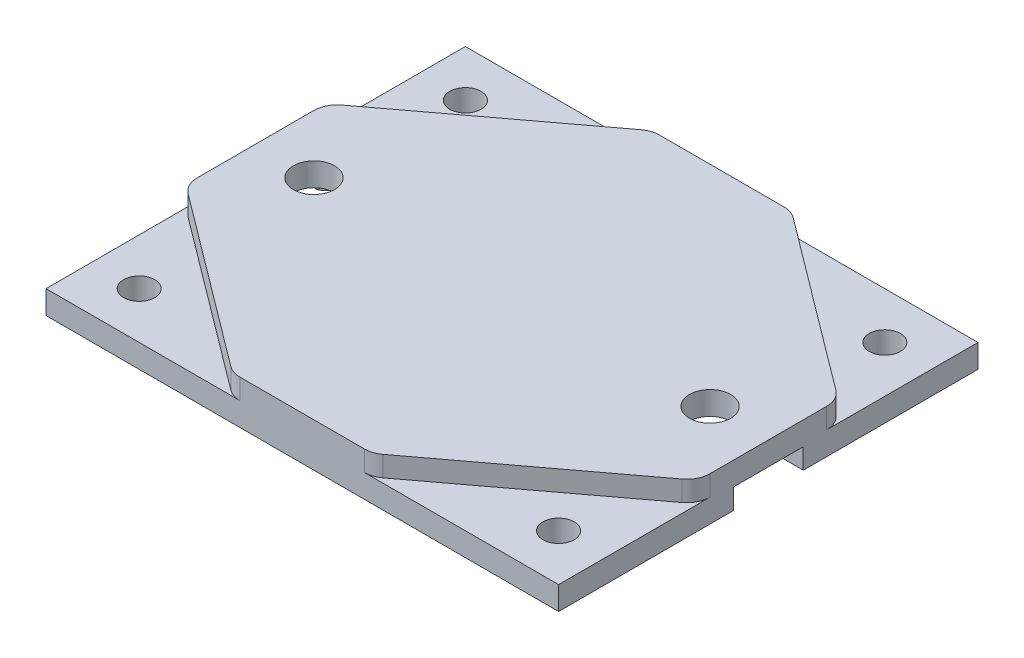
SolidWorks part; units mm, degrees
ref_plane "Front Plane" through (0, 0, 0) normal (0, 0, 1) x (1, 0, 0)
ref_plane "Top Plane" through (0, 0, 0) normal (0, 1, 0) x (1, 0, 0)
ref_plane "Right Plane" through (0, 0, 0) normal (1, 0, 0) x (0, 0, -1)
sketch "Sketch1" plane through (0, 0, 0) normal (0, 1, 0) x (1, 0, 0)
  line L1 (0, 0) -> (55.88, 0)
  line L2 (0, 0) -> (0, 45.72)
  line L3 (0, 45.72) -> (55.88, 45.72)
  line L4 (55.88, 0) -> (55.88, 45.72)
  dimension "D1" = 55.88
  dimension "D2" = 45.72
extrude "Boss-Extrude1" add sketch "Sketch1" along normal blind 2.54
sketch "Sketch2" plane through (0, 2.54, 0) normal (0, 1, 0) x (1, 0, 0)
  line L0 (0, 45.72) -> (0, 0) construction
  line L1 (5.08, 40.64) -> (50.8, 40.64) construction
  line L2 (5.08, 40.64) -> (5.08, 5.08) construction
  line L3 (5.08, 5.08) -> (50.8, 5.08) construction
  line L4 (50.8, 40.64) -> (50.8, 5.08) construction
  line L5 (55.88, 0) -> (55.88, 45.72) construction
  line L6 (0, 0) -> (55.88, 0) construction
  line L7 (55.88, 45.72) -> (0, 45.72) construction
  circle A0 centre (5.08, 40.64) radius 1.7
  circle A1 centre (50.8, 40.64) radius 1.7
  circle A2 centre (50.8, 5.08) radius 1.7
  circle A3 centre (5.08, 5.08) radius 1.7
  dimension "D1" = 3.4
  dimension "D2" = 3.4
  dimension "D3" = 3.4
  dimension "D4" = 3.4
  dimension "D5" = 5.08
  dimension "D6" = 5.08
  dimension "D7" = 5.08
  dimension "D8" = 5.08
extrude "Cut-Extrude1" cut sketch "Sketch2" against normal up to next
sketch "Sketch4" plane through (0, 2.54, 0) normal (0, 1, 0) x (1, 0, 0)
  line L0 (0, 30.48) -> (20.32, 45.72)
  line L1 (0, 45.72) -> (0, 0) construction
  line L2 (55.88, 45.72) -> (0, 45.72) construction
  line L3 (0, 22.86) -> (55.88, 22.86) construction
  line L4 (55.88, 0) -> (55.88, 45.72) construction
  line L5 (27.94, 45.72) -> (27.94, 0) construction
  line L6 (0, 0) -> (55.88, 0) construction
  line L7 (55.88, 30.48) -> (35.56, 45.72)
  line L8 (55.88, 15.24) -> (35.56, 0)
  line L9 (0, 15.24) -> (20.32, 0)
  line L10 (0, 30.48) -> (0, 15.24)
  line L11 (20.32, 0) -> (35.56, 0)
  line L12 (55.88, 15.24) -> (55.88, 30.48)
  line L13 (35.56, 45.72) -> (20.32, 45.72)
  dimension "D1" = 20.32
  dimension "D2" = 15.24
extrude "Boss-Extrude2" add sketch "Sketch4" along normal blind 2.22
sketch "Sketch5" plane through (0, 0, 0) normal (0, -1, 0) x (1, 0, 0)
  line L0 (0, -22.86) -> (55.88, -22.86) construction
  line L1 (0, -45.72) -> (0, 0) construction
  line L2 (55.88, 0) -> (55.88, -45.72) construction
  line L3 (27.94, 0) -> (27.94, -45.72) construction
  line L4 (0, 0) -> (55.88, 0) construction
  line L5 (55.88, -45.72) -> (0, -45.72) construction
  line L6 (3.0629, -18.9868) -> (15.6135, -8.3355)
  line L7 (3.0629, -26.7332) -> (15.6135, -37.3845)
  line L8 (52.8171, -26.7332) -> (40.2665, -37.3845)
  line L9 (52.8171, -18.9868) -> (40.2665, -8.3355)
  circle A0 centre (27.94, -22.86) radius 19.05 construction
  circle A1 centre (6.35, -22.86) radius 5.08 construction
  arc A2 (3.0629, -26.7332) -> (3.0629, -18.9868) centre (6.35, -22.86) cw
  arc A3 (15.6135, -37.3845) -> (40.2665, -37.3845) centre (27.94, -22.86) ccw
  arc A4 (15.6135, -8.3355) -> (40.2665, -8.3355) centre (27.94, -22.86) cw
  arc A5 (52.8171, -26.7332) -> (52.8171, -18.9868) centre (49.53, -22.86) ccw
  point P23 (3.6606, -20.1613)
  point P24 (3.6594, -20.1625)
  dimension "D1" = 38.1
  dimension "D2" = 21.59
  dimension "D3" = 10.16
extrude "Cut-Extrude2" cut sketch "Sketch5" against normal offset from surface (2.22 mm away) 2.54 up to face at (27.94, 4.76, -22.86)
sketch "Sketch6" plane through (0, 4.76, 0) normal (0, 1, 0) x (1, 0, 0)
  line L0 (0, 22.86) -> (55.88, 22.86) construction
  line L1 (0, 30.48) -> (0, 15.24) construction
  line L2 (55.88, 15.24) -> (55.88, 30.48) construction
  line L3 (27.94, 45.72) -> (27.94, 0) construction
  line L4 (35.56, 45.72) -> (20.32, 45.72) construction
  line L5 (20.32, 0) -> (35.56, 0) construction
  circle A0 centre (6.35, 22.86) radius 2.25
  circle A2 centre (49.53, 22.86) radius 2.25
  dimension "D1" = 4.5
  dimension "D2" = 21.59
extrude "Cut-Extrude3" cut sketch "Sketch6" against normal up to next
sketch "Sketch7" plane through (0, 0, 0) normal (-1, 0, 0) x (0, 0, 1)
  line L0 (-22.86, 4.76) -> (-22.86, 0) construction
  line L1 (-30.48, 4.76) -> (-15.24, 4.76) construction
  line L2 (-45.72, 0) -> (0, 0) construction
  line L3 (-15.24, 4.76) -> (-15.24, 2.54) construction
  line L4 (-26.67, 0) -> (-19.05, 0)
  line L5 (-26.67, 0) -> (-26.67, 2.22)
  line L6 (-26.67, 2.22) -> (-19.05, 2.22)
  line L7 (-19.05, 0) -> (-19.05, 2.22)
  line L8 (-30.48, 4.76) -> (-30.48, 2.54) construction
  dimension "D1" = 2.54
  dimension "D2" = 3.81
  dimension "D3" = 3.81
extrude "Cut-Extrude4" cut sketch "Sketch7" against normal through all
fillet "Fillet1" radius 2.54 8 edges at (0, 3.65, -15.24) (0, 3.65, -30.48) (20.32, 3.65, 0) (35.56, 3.65, 0) (55.88, 3.65, -15.24) (55.88, 3.65, -30.48) (20.32, 3.65, -45.72) (35.56, 3.65, -45.72)
